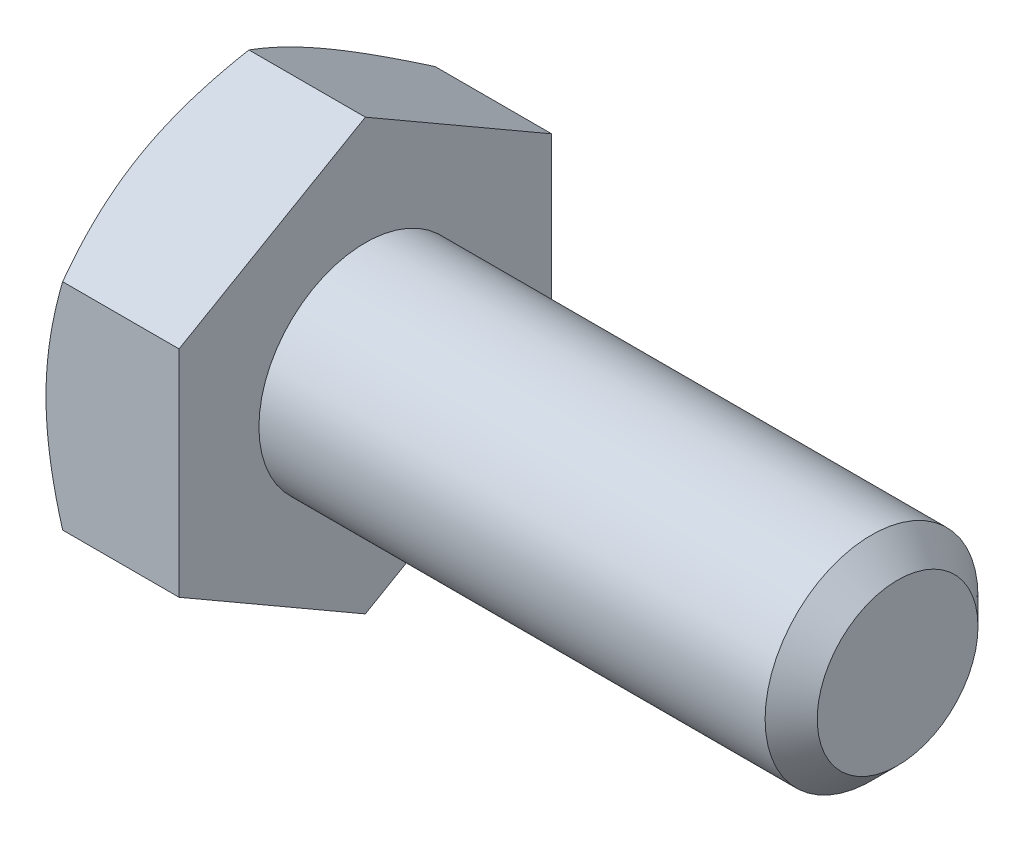
SolidWorks part; units mm, degrees
material "Alloy Steel"
ref_plane "Front Plane" through (0, 0, 0) normal (0, 0, 1) x (1, 0, 0)
ref_plane "Top Plane" through (0, 0, 0) normal (0, 1, 0) x (1, 0, 0)
ref_plane "Right Plane" through (0, 0, 0) normal (1, 0, 0) x (0, 0, -1)
sketch "Sketch1" plane through (0, 0, 0) normal (0, 0, 1) x (1, 0, 0)
  line L0 (-9.9219, 0) -> (9.9219, 0) construction
  line L1 (9.9219, 3.175) -> (9.9219, -3.175) construction
  line L2 (-5.9531, 5.5562) -> (-5.9531, -5.5562) construction
  line L3 (-9.9219, 5.5562) -> (-9.9219, -5.5562) construction
  point P9 (-5.9531, 0)
  point P10 (5.4769, -3.175)
  dimension "D1" = 4.445
  dimension "Screw Dia" = 6.35
  dimension "Hex" = 11.1125
  dimension "Head Ht" = 3.9688
  dimension "Screw Lenght" = 15.875
ref_plane "Plane2" through (9.9219, 0, 0) normal (1, 0, 0) x (0, 0, -1)
sketch "Sketch5" plane through (9.9219, 0, 0) normal (1, 0, 0) x (0, 0, -1)
  circle A0 centre (0, 0) radius 3.175
extrude "Boss-Extrude3" add sketch "Sketch5" against normal up to vertex (15.875 mm away) up to point (-5.9531, 0, 0)
sketch "Sketch9" plane through (9.9219, 0, 0) normal (1, 0, 0) x (0, 0, -1)
  circle A1 centre (0, 0) radius 3.175
  circle A2 centre (0, 0) radius 3.175
  dimension "D1" = 0
curve "Helix/Spiral1" pitch 1.27 height 17.145 turns 13.5 parameters "Pitch"=1.27
chamfer "Chamfer1" distance 0.7772 angle 45 1 edges at (9.9219, 0, -3.175)
sketch "Sketch10" plane through (0, 0, 0) normal (0, 0, 1) x (1, 0, 0)
  line L0 (9.9219, 3.175) -> (10.3981, 2.3501)
  line L1 (10.3981, 2.3501) -> (10.5569, 2.3501)
  line L2 (10.5569, 2.3501) -> (11.0331, 3.175)
  line L3 (9.9219, 3.175) -> (11.0331, 3.175)
  line L4 (10.4775, 3.175) -> (10.4775, 2.3501) construction
  line L5 (10.16, 2.7626) -> (10.795, 2.7626) construction
  dimension "D1" = 60
  dimension "D2" = 0.1588
  dimension "D3" = 0.635
sketch "Sketch6" plane through (-5.9531, 0, 0) normal (-1, 0, 0) x (0, 0, 1)
  line L0 (0, 5.5562) -> (0, -5.5562) construction
  line L1 (5.5563, 3.2079) -> (0, 6.4158)
  line L2 (0, 6.4158) -> (-5.5562, 3.2079)
  line L3 (-5.5562, 3.2079) -> (-5.5562, -3.2079)
  line L4 (-5.5562, -3.2079) -> (0, -6.4158)
  line L5 (0, -6.4158) -> (5.5563, -3.2079)
  line L6 (5.5563, -3.2079) -> (5.5563, 3.2079)
  circle A0 centre (0, 0) radius 5.5563 construction
extrude "Boss-Extrude4" add sketch "Sketch6" along normal up to vertex (3.9688 mm away) up to point (-9.9219, -5.5562, 0)
sketch "Sketch7" plane through (-9.9219, 0, 0) normal (-1, 0, 0) x (0, 0, 1)
  circle A0 centre (0, 0) radius 5.5563 construction
  circle A1 centre (0, 0) radius 5.5563
sketch "Sketch8" plane through (-9.9219, 0, 0) normal (-1, 0, 0) x (0, 0, 1)
  circle A0 centre (0, 0) radius 5.5563 construction
  circle A1 centre (0, 0) radius 5.5563
extrude "Cut-Extrude3" cut sketch "Sketch8" against normal through all draft 60 flip side to cut
sketch "Sketch12" plane through (-9.9219, 0, 0) normal (-1, 0, 0) x (0, 0, 1)
  line L0 (0, 4.2783) -> (0, 2.3892) construction
  line L1 (0.1667, 4.2783) -> (0.1667, 2.3892)
  line L2 (-0.1667, 4.2783) -> (-0.1667, 2.3892)
  line L3 (0, 3.175) -> (0, -3.175) construction
  arc A0 (0.1667, 4.2783) -> (-0.1667, 4.2783) centre (0, 4.2783) ccw
  arc A1 (-0.1667, 2.3892) -> (0.1667, 2.3892) centre (0, 2.3892) ccw
  circle A3 centre (0, 0) radius 2.2225 construction
  circle A4 centre (0, 0) radius 4.445 construction
  point P2 (0, 3.3337)
  dimension "D1" = 4.445
  dimension "D3" = 8.89
  dimension "D2" = 0.3334
extrude "Cut-Extrude4" cut sketch "Sketch12" against normal blind 0.254
pattern_circular "CirPattern1" count 3 over 360 about axis through (0, 0, 0) along (1, 0, 0) of "Cut-Extrude4"
equation "\"D2@Sketch10\" = \"Pitch@Helix/Spiral1\"*.125"
equation "\"D3@Sketch10\" = \"Pitch@Helix/Spiral1\"*.5"
equation "\"D1@Chamfer1\" = \"Pitch@Helix/Spiral1\"*.612"
equation "\"D1@Sketch12\" = \"Hex@Sketch1\"*.4"
equation "\"D3@Sketch12\" = \"Hex@Sketch1\"*.8"
equation "\"D2@Sketch12\" = \"Hex@Sketch1\"*.03"
equation "\"D1@Sketch1\" = \"Pitch@Helix/Spiral1\"*3.5"
equation "\"D3@Helix/Spiral1\" = \"Screw Lenght@Sketch1\"+\"Pitch@Helix/Spiral1\""
